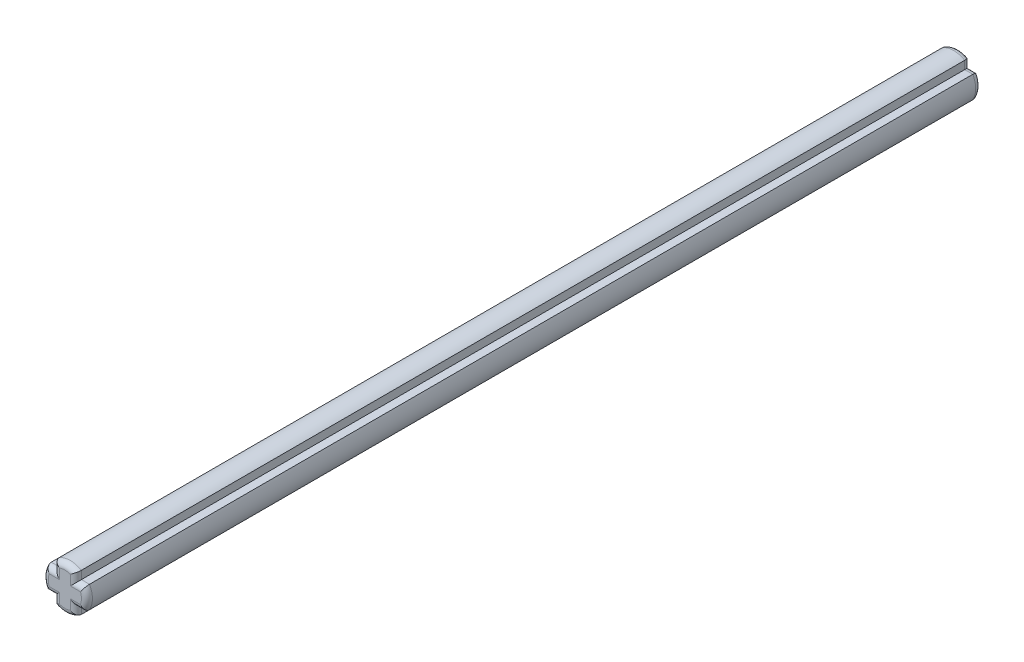
SolidWorks part; units mm, degrees
ref_plane "Front Plane" through (0, 0, 0) normal (0, 0, 1) x (1, 0, 0)
ref_plane "Top Plane" through (0, 0, 0) normal (0, 1, 0) x (1, 0, 0)
ref_plane "Right Plane" through (0, 0, 0) normal (1, 0, 0) x (0, 0, -1)
sketch "Sketch1" plane through (0, 0, 0) normal (0, 0, 1) x (1, 0, 0)
  line L0 (-1, 1) -> (-1, 2)
  line L1 (-1, -2) -> (1, -2)
  line L2 (-1, -2) -> (-1, -1)
  line L3 (-1, 2) -> (1, 2)
  line L4 (1, -2) -> (1, -1)
  line L5 (-1, -2) -> (1, 2) construction
  line L6 (-1, 2) -> (1, -2) construction
  line L7 (-2, 1) -> (-1, 1)
  line L8 (-2, 1) -> (-2, -1)
  line L9 (-2, -1) -> (-1, -1)
  line L10 (2, 1) -> (2, -1)
  line L11 (-2, 1) -> (2, -1) construction
  line L12 (-2, -1) -> (2, 1) construction
  line L13 (1, 1) -> (2, 1)
  line L14 (1, 1) -> (1, 2)
  line L15 (1, -1) -> (2, -1)
  point P0 (0, 0)
  point P6 (0, 0)
  dimension "D1" = 2
  dimension "D2" = 4
  dimension "D3" = 4
extrude "Boss-Extrude1" add sketch "Sketch1" along normal blind 81
sketch "Sketch2" plane through (0, 0, 0) normal (0, 0, 1) x (1, 0, 0)
  circle A0 centre (0, 0) radius 2
  dimension "D1" = 4
extrude "Cut-Extrude3" cut sketch "Sketch2" along normal through all flip side to cut
fillet "Fillet1" radius 0.5 24 edges at (-1.366, -1, 81) (-2, 0, 81) (-1.366, 1, 81) (-1, 1.366, 81) (0, 2, 81) (1, 1.366, 81) (1.366, 1, 81) (2, 0, 81) (1.366, -1, 81) (1, -1.366, 81) (0, -2, 81) (-1, -1.366, 81) (1, -1.366, 0) (1.366, -1, 0) (2, 0, 0) (1.366, 1, 0) (1, 1.366, 0) (0, 2, 0) (-1, 1.366, 0) (-1.366, 1, 0) (-2, 0, 0) (-1.366, -1, 0) (-1, -1.366, 0) (0, -2, 0)
